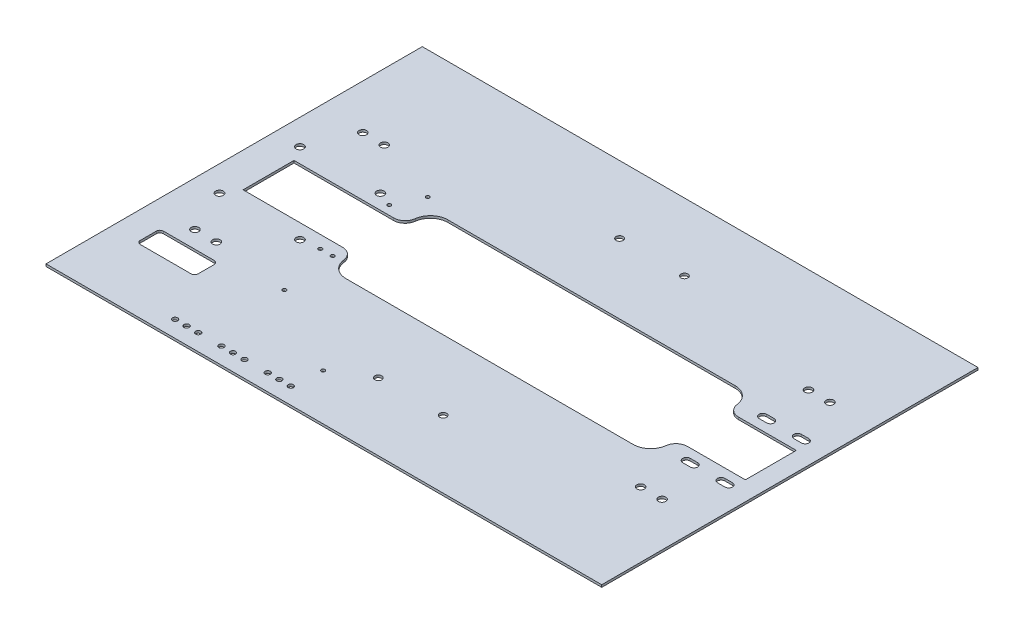
SolidWorks part; units mm, degrees
ref_plane "Front Plane" through (0, 0, 0) normal (0, 0, 1) x (1, 0, 0)
ref_plane "Top Plane" through (0, 0, 0) normal (0, 1, 0) x (1, 0, 0)
ref_plane "Right Plane" through (0, 0, 0) normal (1, 0, 0) x (0, 0, -1)
sketch "Sketch1" plane through (0, 0, 0) normal (0, 1, 0) x (1, 0, 0)
  line L1 (-240, 162.5) -> (240, 162.5)
  line L2 (-240, 162.5) -> (-240, -162.5)
  line L3 (-240, -162.5) -> (240, -162.5)
  line L4 (240, 162.5) -> (240, -162.5)
  line L5 (-240, 162.5) -> (240, -162.5) construction
  line L6 (-240, -162.5) -> (240, 162.5) construction
  point P0 (0, 0)
  dimension "D1" = 480
  dimension "D2" = 325
extrude "Boss-Extrude1" add sketch "Sketch1" along normal blind 2
sketch "Sketch2" plane through (0, 0, 0) normal (0, -1, 0) x (1, 0, 0)
  circle A0 centre (44.7486, -104.2) radius 3
  circle A1 centre (-11.2514, -104.2) radius 3
  circle A2 centre (44.7486, 104.2) radius 3
  circle A3 centre (-11.2514, 104.2) radius 3
extrude "Cut-Extrude1" cut sketch "Sketch2" against normal up to next
sketch "Sketch3" plane through (0, 0, 0) normal (0, -1, 0) x (1, 0, 0)
  line L0 (-192.4406, 0) -> (188.5847, 0) construction
  line L1 (163.5847, 44) -> (-114.2887, 44)
  line L2 (163.5847, 44) -> (163.5847, 22)
  line L3 (163.5847, -44) -> (-114.2887, -44)
  line L5 (-114.2887, -44) -> (-114.2887, -22)
  line L6 (-114.2887, -22) -> (-210.2887, -22)
  line L7 (-114.2887, 44) -> (-114.2887, 22)
  line L8 (-114.2887, 22) -> (-210.2887, 22)
  line L9 (-210.2887, 22) -> (-210.2887, -22)
  line L10 (163.5847, 22) -> (223.5847, 22)
  line L11 (223.5847, 22) -> (223.5847, -22)
  line L12 (223.5847, -22) -> (163.5847, -22)
  line L13 (163.5847, -22) -> (163.5847, -44)
  point P0 (0, 0)
  point P1 (-210.2887, 0)
  dimension "D2" = 96
  dimension "D1" = 22
  dimension "D5" = 60
extrude "Cut-Extrude2" cut sketch "Sketch3" against normal up to next
fillet "Fillet1" radius 10 2 edges at (-114.2887, 1, 22) (-114.2887, 1, -22)
sketch "Sketch4" plane through (0, 0, 0) normal (0, -1, 0) x (1, 0, 0)
  circle A12 centre (-148.4257, -34.75) radius 3.3
  circle A13 centre (-148.4257, 34.75) radius 3.3
  circle A14 centre (-217.9257, 34.75) radius 3.3
  circle A15 centre (-217.9257, -34.75) radius 3.3
extrude "Cut-Extrude3" cut sketch "Sketch4" against normal up to next
fillet "Fillet2" radius 10 2 edges at (163.5847, 1, -22) (163.5847, 1, 22)
sketch "Sketch12" plane through (0, 0, 0) normal (0, -1, 0) x (1, 0, 0)
  circle A0 centre (-135.7811, -29.7616) radius 1.5
  circle A1 centre (-125.1811, -52.3616) radius 1.5
extrude "Cut-Extrude11" cut sketch "Sketch12" against normal up to next
fillet "Fillet3" radius 15 4 edges at (163.5847, 1, 44) (163.5847, 1, -44) (-114.2887, 1, 44) (-114.2887, 1, -44)
sketch "Sketch14" plane through (0, 2, 0) normal (0, 1, 0) x (1, 0, 0)
  line L1 (-213.8384, -87.2865) -> (-169.8384, -87.2865)
  line L2 (-216.8384, -90.2865) -> (-216.8384, -104.2865)
  line L3 (-213.8384, -107.2865) -> (-169.8384, -107.2865)
  line L4 (-166.8384, -90.2865) -> (-166.8384, -104.2865)
  arc A0 (-169.8384, -87.2865) -> (-166.8384, -90.2865) centre (-169.8384, -90.2865) cw
  arc A1 (-169.8384, -107.2865) -> (-166.8384, -104.2865) centre (-169.8384, -104.2865) ccw
  arc A2 (-216.8384, -104.2865) -> (-213.8384, -107.2865) centre (-213.8384, -104.2865) ccw
  arc A3 (-213.8384, -87.2865) -> (-216.8384, -90.2865) centre (-213.8384, -90.2865) ccw
  point P8 (-166.8384, -107.2865)
  point P11 (-216.8384, -107.2865)
  point P14 (-216.8384, -87.2865)
  dimension "D3" = 3
  dimension "D1" = 50
  dimension "D2" = 20
extrude "Cut-Extrude13" cut sketch "Sketch14" against normal through all
sketch "Sketch15" plane through (0, 2, 0) normal (0, 1, 0) x (1, 0, 0)
  line L0 (-201.3752, -109.7364) -> (-201.3752, 118.5225) construction
  line L1 (-182.8647, -109.7364) -> (-182.8647, 113.1876) construction
  line L2 (-257.879, -72.5) -> (-138.224, -72.5) construction
  line L3 (-257.879, 72.5) -> (-138.224, 72.5) construction
  line L4 (183.6248, -104.4043) -> (183.6248, 127.2576) construction
  line L5 (202.1353, -104.4043) -> (202.1353, 113.1876) construction
  line L6 (152.11, 72.5) -> (276.9157, 72.5) construction
  line L7 (152.11, -72.5) -> (265.9977, -72.5) construction
  circle A8 centre (-201.3752, -72.5) radius 3.25
  circle A9 centre (-182.8647, -72.5) radius 3.25
  circle A10 centre (-201.3752, 72.5) radius 3.25
  circle A11 centre (-182.8647, 72.5) radius 3.25
  circle A12 centre (183.6248, 72.5) radius 3.25
  circle A13 centre (202.1353, 72.5) radius 3.25
  circle A14 centre (183.6248, -72.5) radius 3.25
  circle A15 centre (202.1353, -72.5) radius 3.25
extrude "Cut-Extrude14" cut sketch "Sketch15" against normal up to next
sketch "Sketch16" plane through (0, 2, 0) normal (0, 1, 0) x (1, 0, 0)
  line L0 (183.6729, -33) -> (186.9229, -33) construction
  line L1 (213.6729, -33) -> (216.9229, -33) construction
  line L2 (183.6729, 33) -> (186.9229, 33) construction
  line L3 (213.6729, 33) -> (216.9229, 33) construction
  line L4 (183.6729, -36.25) -> (190.1729, -36.25)
  line L5 (183.6729, -29.75) -> (190.1729, -29.75)
  line L6 (213.6729, -36.25) -> (220.1729, -36.25)
  line L7 (213.6729, -29.75) -> (220.1729, -29.75)
  line L8 (183.6729, 29.75) -> (190.1729, 29.75)
  line L9 (183.6729, 36.25) -> (190.1729, 36.25)
  line L10 (213.6729, 29.75) -> (220.1729, 29.75)
  line L11 (213.6729, 36.25) -> (220.1729, 36.25)
  arc A4 (213.6729, -29.75) -> (213.6729, -36.25) centre (213.6729, -33) ccw
  arc A5 (183.6729, -29.75) -> (183.6729, -36.25) centre (183.6729, -33) ccw
  arc A6 (183.6729, 36.25) -> (183.6729, 29.75) centre (183.6729, 33) ccw
  arc A7 (213.6729, 36.25) -> (213.6729, 29.75) centre (213.6729, 33) ccw
  arc A8 (190.1729, -36.25) -> (190.1729, -29.75) centre (190.1729, -33) ccw
  arc A9 (220.1729, -36.25) -> (220.1729, -29.75) centre (220.1729, -33) ccw
  arc A10 (220.1729, 29.75) -> (220.1729, 36.25) centre (220.1729, 33) ccw
  arc A11 (190.1729, 29.75) -> (190.1729, 36.25) centre (190.1729, 33) ccw
  dimension "D1" = 6.5
  dimension "D2" = 6.5
  dimension "D3" = 6.5
  dimension "D4" = 6.5
extrude "Cut-Extrude15" cut sketch "Sketch16" against normal up to next
sketch "Sketch17" plane through (0, 0, 0) normal (0, -1, 0) x (1, 0, 0)
  circle A0 centre (-40.5895, 122.5729) radius 1.6
  circle A1 centre (-117.4629, 79.1007) radius 1.6
  circle A2 centre (-132.736, 32.8078) radius 1.6
  circle A3 centre (-122.117, 32.8078) radius 1.6
extrude "Cut-Extrude16" cut sketch "Sketch17" against normal up to next
sketch "Sketch18" plane through (0, 0, 0) normal (0, -1, 0) x (1, 0, 0)
  line L0 (-26.7322, 148.2204) -> (-158.3005, 148.2204) construction
  circle A0 centre (-42.7844, 148.2204) radius 2.25
  circle A1 centre (-52.7844, 148.2204) radius 2.25
  circle A2 centre (-62.7844, 148.2204) radius 2.25
  circle A3 centre (-82.7844, 148.2204) radius 2.25
  circle A4 centre (-92.7844, 148.2204) radius 2.25
  circle A5 centre (-102.7844, 148.2204) radius 2.25
  circle A6 centre (-122.7844, 148.2204) radius 2.25
  circle A7 centre (-132.7844, 148.2204) radius 2.25
  circle A8 centre (-142.7844, 148.2204) radius 2.25
  dimension "D1" = 4.5
  dimension "D2" = 10
  dimension "D3" = 10
  dimension "D4" = 10
  dimension "D5" = 10
  dimension "D6" = 20
  dimension "D7" = 20
  dimension "D8" = 10
  dimension "D9" = 10
extrude "Cut-Extrude17" cut sketch "Sketch18" against normal up to next
